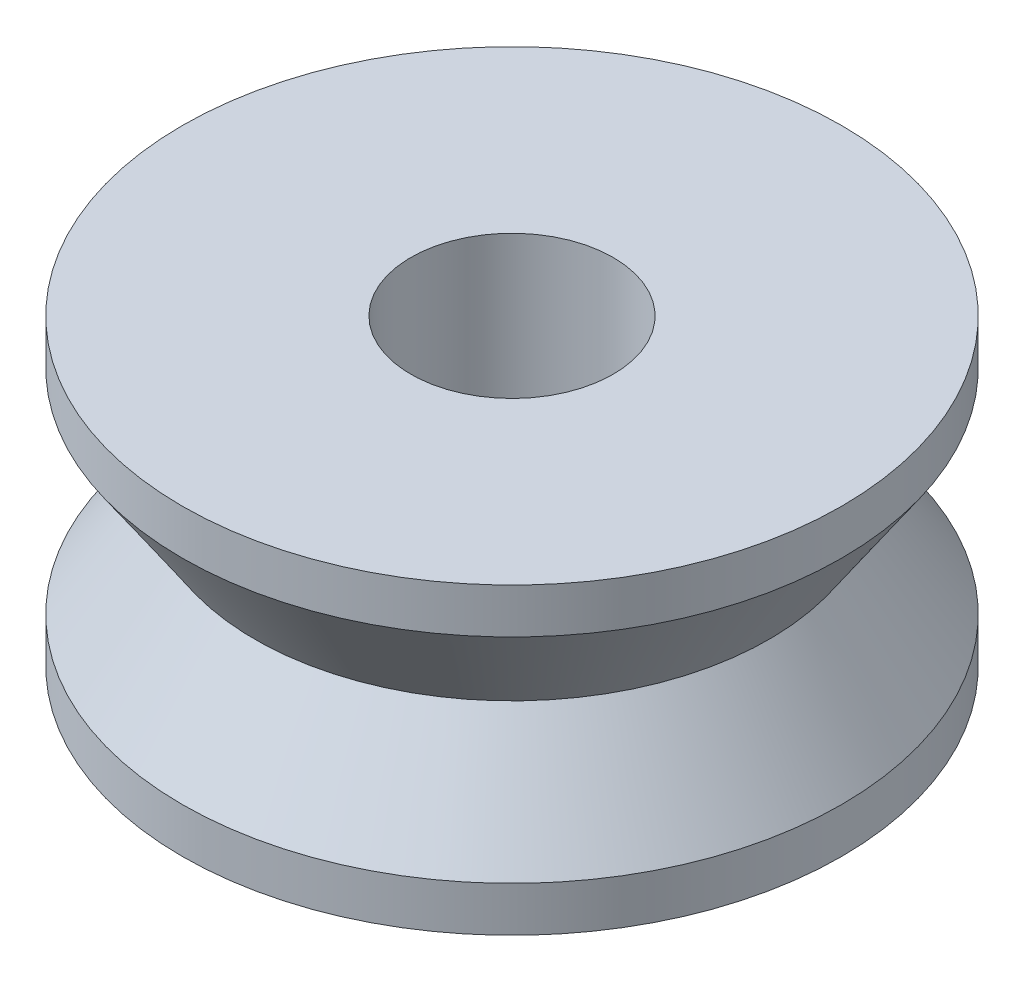
SolidWorks part; units mm, degrees
ref_plane "Front Plane" through (0, 0, 0) normal (0, 0, 1) x (1, 0, 0)
ref_plane "Top Plane" through (0, 0, 0) normal (0, 1, 0) x (1, 0, 0)
ref_plane "Right Plane" through (0, 0, 0) normal (1, 0, 0) x (0, 0, -1)
sketch "Sketch1" plane through (0, 0, 0) normal (0, 0, 1) x (1, 0, 0)
  line L0 (-6.5151, -2.9972) -> (6.5151, -2.9972)
  line L1 (6.5151, -2.9972) -> (6.5151, -2.1082)
  line L2 (6.5151, -2.1082) -> (5.08, 0)
  line L3 (-6.5151, -2.9972) -> (-6.5151, -2.1082)
  line L4 (-6.5151, -2.1082) -> (-5.08, 0)
  line L5 (-5.08, 0) -> (0, 0) construction
  line L6 (6.5151, 2.9972) -> (6.5151, 2.1082)
  line L7 (6.5151, 2.1082) -> (5.08, 0)
  line L8 (-6.5151, 2.9972) -> (6.5151, 2.9972)
  line L9 (-6.5151, 2.9972) -> (-6.5151, 2.1082)
  line L10 (-6.5151, 2.1082) -> (-5.08, 0)
  line L11 (0, 0) -> (5.08, 0) construction
  line L12 (0, 0) -> (0, 2.9972) construction
  line L13 (0, 0) -> (0, -2.9972) construction
  line L14 (6.5151, 2.5527) -> (0, 2.5527) construction
  line L15 (0, 2.5527) -> (-6.5151, 2.5527) construction
  line L16 (0, 2.9972) -> (0, -2.9972) construction
  line L17 (-2, 2.9972) -> (-2, -2.9972)
  dimension "D1" = 13.0302
  dimension "D2" = 0.889
  dimension "D3" = 5.9944
  dimension "D4" = 4.2164
  dimension "D5" = 10.16
  dimension "D6" = 2
revolve "Revolve2" add sketch "Sketch1" angle 360 about L12
